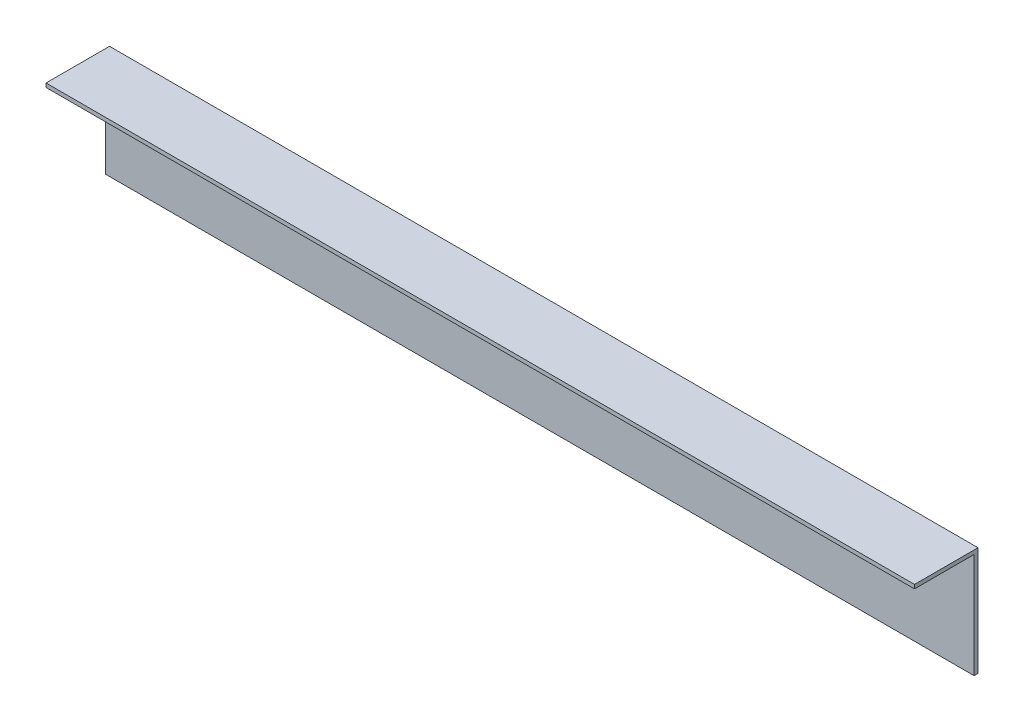
SolidWorks part; units mm, degrees
ref_plane "前基準面" through (0, 0, 0) normal (0, 0, 1) x (1, 0, 0)
ref_plane "上基準面" through (0, 0, 0) normal (0, 1, 0) x (1, 0, 0)
ref_plane "右基準面" through (0, 0, 0) normal (1, 0, 0) x (0, 0, -1)
sketch "草圖1" plane through (0, 0, 0) normal (0, 0, 1) x (1, 0, 0)
  line L1 (-158.4364, -26.5105) -> (176.5636, -26.5105)
  line L2 (-158.4364, -26.5105) -> (-158.4364, -68.5105)
  line L3 (-158.4364, -68.5105) -> (176.5636, -68.5105)
  line L4 (176.5636, -26.5105) -> (176.5636, -68.5105)
  dimension "D1" = 335
  dimension "D2" = 42
extrude "填料-伸長1" add sketch "草圖1" along normal blind 1.5 contours L1 L4 L3 L2
sketch "草圖2" plane through (0, 0, 1.5) normal (0, 0, 1) x (1, 0, 0)
  line L0 (176.5636, -26.5105) -> (176.5636, -68.5105) construction
  line L1 (-158.4364, -26.5105) -> (176.5636, -26.5105)
  line L2 (-158.4364, -26.5105) -> (-158.4364, -28.0105)
  line L3 (-158.4364, -28.0105) -> (176.5636, -28.0105)
  line L4 (176.5636, -26.5105) -> (176.5636, -28.0105)
  dimension "D1" = 1.5
extrude "填料-伸長2" add sketch "草圖2" along normal blind 23
